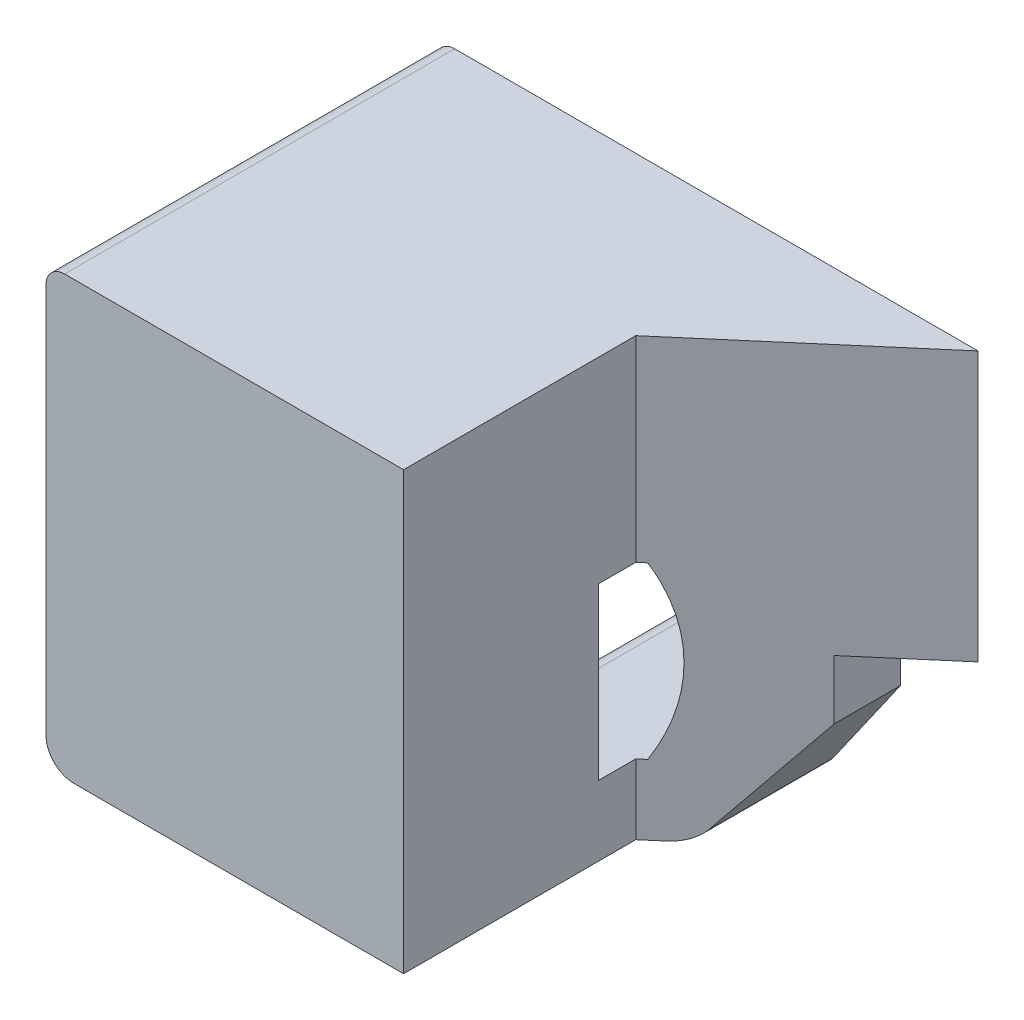
SolidWorks part; units mm, degrees
ref_plane "Front Plane" through (0, 0, 0) normal (0, 0, 1) x (1, 0, 0)
ref_plane "Top Plane" through (0, 0, 0) normal (0, 1, 0) x (1, 0, 0)
ref_plane "Right Plane" through (0, 0, 0) normal (1, 0, 0) x (0, 0, -1)
sketch "Sketch1" plane through (0, 0, 0) normal (0, 0, 1) x (1, 0, 0)
  line L1 (-14.859, 11.938) -> (0, 11.938)
  line L2 (-14.859, 11.938) -> (-14.859, 0)
  line L3 (-14.859, 0) -> (-3.175, 0)
  line L4 (0, 11.938) -> (0, 4.572)
  line L7 (0, 4.572) -> (-3.175, 4.572)
  line L8 (-3.175, 0) -> (-3.175, 4.572)
  dimension "D1" = 11.684
  dimension "D2" = 7.366
  dimension "D3" = 14.859
  dimension "D4" = 11.938
extrude "Extrude1" add sketch "Sketch1" against normal blind 4.7752
sketch "Sketch2" plane through (0, 11.938, 0) normal (0, 1, 0) x (1, 0, 0)
  line L0 (0, 0.5842) -> (-4.191, 4.7752)
  line L1 (0, 4.7752) -> (0, 0) construction
  line L2 (0, 4.7752) -> (-14.859, 4.7752) construction
  line L3 (-4.191, 4.7752) -> (0, 4.7752)
  line L4 (0, 4.7752) -> (0, 0.5842)
  dimension "D1" = 45
  dimension "D2" = 0.5842
extrude "Extrude2" cut sketch "Sketch2" against normal through all
sketch "Sketch33" plane through (-14.859, 0, 0) normal (-1, 0, 0) x (0, 0, 1)
  line L1 (-4.7752, 11.938) -> (-7.0612, 11.938)
  line L2 (-4.7752, 11.938) -> (-4.7752, 6.35)
  line L3 (-4.7752, 6.35) -> (-7.0612, 6.35)
  line L4 (-7.0612, 11.938) -> (-7.0612, 6.35)
  dimension "D1" = 5.588
  dimension "D2" = 2.286
extrude "Extrude30" add sketch "Sketch33" against normal up to vertex (10.668 mm away) up to point (-4.191, 11.938, -4.7752)
sketch "Unlocked" plane through (0, 0, 0) normal (0, 0, 1) x (1, 0, 0)
  circle A0 centre (-9.7028, 4.2418) radius 4.191
  dimension "D3" = 8.382
  dimension "D1" = 2.1082
  dimension "D2" = 5.1562
sketch "End Pressure" plane through (0, 0, 0) normal (0, 0, 1) x (1, 0, 0)
  circle A0 centre (-11.4808, 4.2418) radius 4.191
  dimension "D2" = 8.382
  dimension "D1" = 1.778
sketch "No End Pressure" plane through (0, 0, 0) normal (0, 0, 1) x (1, 0, 0)
  circle A0 centre (-11.9888, 4.2418) radius 4.191
  dimension "D1" = 8.382
  dimension "D2" = 0.508
sketch "Wide Arc" plane through (0, 0, 0) normal (0, 0, 1) x (1, 0, 0)
  circle A10 centre (-11.4808, 4.2418) radius 4.572
  arc A11 (-11.7348, -0.3231) -> (-11.7348, 8.8067) centre (-11.4808, 4.2418) ccw
  circle A13 centre (-11.9888, 4.2418) radius 4.572
  arc A14 (-11.7348, 8.8067) -> (-11.7348, -0.3231) centre (-11.9888, 4.2418) ccw
  dimension "D1" = 0.381
  dimension "D2" = 0.381
sketch "Sketch5" plane through (0, 0, 0) normal (0, 0, 1) x (1, 0, 0)
  line L0 (-14.859, 0) -> (-3.175, 0) construction
  line L1 (-8.962, -0.141) -> (-11.1845, -0.5167) construction
  line L2 (-9.0043, 0.1094) -> (-11.2268, -0.2663) construction
  line L5 (-14.859, 11.938) -> (-14.859, 0) construction
  line L8 (-14.859, 8.1215) -> (-14.859, 0)
  line L9 (-14.859, 0) -> (-8.3742, 0)
  circle A0 centre (-9.7028, 4.2418) radius 4.191 construction
  arc A1 (-9.0043, 0.1094) -> (-8.3436, 8.2063) centre (-9.7028, 4.2418) ccw construction
  arc A2 (-8.3742, 0) -> (-8.2612, 8.4465) centre (-9.7028, 4.2418) ccw
  arc A3 (-8.3436, 8.2063) -> (-11.9888, 8.8138) centre (-11.9888, -2.4257) ccw construction
  arc A4 (-11.7348, 8.8067) -> (-11.7348, -0.3231) centre (-11.9888, 4.2418) ccw construction
  arc A5 (-8.2612, 8.4465) -> (-11.9888, 9.0678) centre (-11.9888, -2.4257) ccw
  arc A6 (-11.9888, 9.0678) -> (-14.859, 8.1215) centre (-11.9888, 4.2418) ccw
  arc A7 (-11.9888, 8.8138) -> (-11.2268, -0.2663) centre (-11.9888, 4.2418) ccw construction
  arc A9 (-8.962, -0.141) -> (-8.2612, 8.4465) centre (-9.7028, 4.2418) ccw construction
  dimension "D1" = 0.254
extrude "Extrude3" cut sketch "Sketch5" against normal blind 3.0988
sketch "Sketch8" plane through (0, 0, 0) normal (0, 0, 1) x (1, 0, 0)
  line L0 (-5.9161, 6.5697) -> (-7.9958, 6.5697)
  line L1 (-8.8371, 7.4938) -> (-8.8371, 8.6017)
  circle A0 centre (-11.4808, 4.2418) radius 4.191 construction
  arc A1 (-7.9958, 6.5697) -> (-8.8371, 7.4938) centre (-11.4808, 4.2418) ccw
  arc A3 (-5.9161, 6.5697) -> (-8.8371, 8.6017) centre (-9.7028, 4.2418) ccw
  arc A5 (-8.3742, 0) -> (-8.2612, 8.4465) centre (-9.7028, 4.2418) ccw construction
  dimension "D1" = 2.921
  dimension "D2" = 2.032
extrude "Extrude6" add sketch "Sketch8" against normal up to surface (3.0988 mm away) up to face at (-11.0666, 5.1959, -3.0988)
sketch "Sketch9" plane through (0, 0, 0) normal (0, 0, 1) x (1, 0, 0)
  line L0 (-5.9161, 1.9139) -> (-7.9958, 1.9139)
  line L1 (-8.8371, 0) -> (-8.8371, 0.9898)
  line L2 (-8.3742, 0) -> (-8.8371, 0)
  line L3 (-8.8371, -0.1181) -> (-8.8371, 0) construction
  arc A0 (-8.3742, 0) -> (-8.8371, -0.1181) centre (-9.7028, 4.2418) cw construction
  circle A1 centre (-11.4808, 4.2418) radius 4.191 construction
  arc A2 (-8.3742, 0) -> (-5.9161, 1.9139) centre (-9.7028, 4.2418) ccw
  arc A3 (-8.8371, 0.9898) -> (-7.9958, 1.9139) centre (-11.4808, 4.2418) ccw
  arc A4 (-8.3742, 0) -> (-5.9161, 6.5697) centre (-9.7028, 4.2418) ccw construction
  dimension "D1" = 2.921
  dimension "D2" = 2.032
extrude "Extrude7" add sketch "Sketch9" against normal up to surface (3.0988 mm away) up to face at (-9.8151, 6.0773, -3.0988)
sketch "Sketch23" plane through (-8.8371, 0, 0) normal (-1, 0, 0) x (0, 0, 1)
  line L0 (-3.0988, 7.4938) -> (-3.0988, 8.6017) construction
  line L1 (0, 7.4938) -> (-3.0988, 7.4938)
  line L2 (0, 7.4938) -> (0, 8.6272)
  line L3 (0, 8.6272) -> (-3.0988, 8.6272)
  line L4 (-3.0988, 7.4938) -> (-3.0988, 8.6272)
  line L7 (-3.0988, 7.4938) -> (0, 7.4938) construction
extrude "Extrude20" add sketch "Sketch23" against normal blind 2.54
sketch "Sketch18" plane through (0, 0, 0) normal (0, 0, 1) x (1, 0, 0)
  line L0 (-4.9036, 6.5697) -> (-5.9161, 6.5697)
  line L1 (-4.9036, 1.9139) -> (-5.9161, 1.9139)
  line L2 (-7.9958, 6.5697) -> (-5.9161, 6.5697) construction
  line L5 (-5.9161, 1.9139) -> (-7.9958, 1.9139) construction
  arc A2 (-4.9036, 1.9139) -> (-4.9036, 6.5697) centre (-9.7028, 4.2418) ccw
  arc A3 (-5.1588, 1.4483) -> (-5.1588, 7.0353) centre (-9.7028, 4.2418) ccw construction
  arc A4 (-5.9161, 1.9139) -> (-5.9161, 6.5697) centre (-9.7028, 4.2418) ccw
  arc A5 (-5.9161, 1.9139) -> (-5.9161, 6.5697) centre (-9.7028, 4.2418) ccw construction
  dimension "D1" = 0.889
extrude "Extrude16" cut sketch "Sketch18" against normal up to surface (3.0988 mm away) up to face at (-9.4738, 4.6916, -3.0988)
fillet "Fillet1" radius 0.762 1 edges at (0, 8.255, -0.5842)
sketch "Sketch24" plane through (0, 0, 0) normal (0, 0, 1) x (1, 0, 0)
  line L0 (-8.8371, 7.4938) -> (-9.8301, 8.3011)
  line L1 (-8.8371, 9.0678) -> (-8.8371, 7.4938)
  line L2 (-8.8371, 8.6272) -> (-8.8371, 7.4938) construction
  line L3 (-8.8371, 9.0678) -> (-11.9888, 9.0678)
  arc A0 (-7.9958, 6.5697) -> (-8.8371, 7.4938) centre (-11.4808, 4.2418) ccw construction
  arc A6 (-9.8301, 8.3011) -> (-11.9888, 9.0678) centre (-11.9888, 5.6457) ccw
  arc A8 (-11.9888, 9.0678) -> (-14.859, 8.1215) centre (-11.9888, 4.2418) ccw construction
extrude "Extrude21" add sketch "Sketch24" against normal up to surface (3.0988 mm away) up to face at (-9.301, 4.6916, -3.0988)
fillet "Fillet2" radius 0.762 1 edges at (-14.859, 0, -3.937)
sketch "Sketch31" plane through (0, 0, 0) normal (0, 0, 1) x (1, 0, 0)
  line L0 (-3.175, 1.4994) -> (-4.2249, 0)
  line L1 (-3.175, 0) -> (-3.175, 4.572) construction
  line L2 (-8.8371, 0) -> (-3.175, 0) construction
  line L3 (-4.2249, 0) -> (-3.175, 0)
  line L4 (-3.175, 0) -> (-3.175, 1.4994)
  line L5 (-3.175, 1.4994) -> (-1.397, 4.0386) construction
  line L7 (-1.397, 4.0386) -> (-1.397, 4.572) construction
  line L8 (-3.175, 4.572) -> (0, 4.572) construction
  dimension "D1" = 55
  dimension "D2" = 1.778
  dimension "D3" = 0.5334
extrude "Extrude28" cut sketch "Sketch31" against normal through all
sketch "Sketch32" plane through (0, 0, 0) normal (0, 0, 1) x (1, 0, 0)
  line L0 (-3.175, 1.4994) -> (-2.159, 2.9504)
  line L1 (-2.159, 2.9504) -> (-2.159, 4.572)
  line L2 (-3.175, 4.572) -> (0, 4.572) construction
  line L3 (-2.159, 4.572) -> (-3.175, 4.572)
  line L4 (-3.175, 4.572) -> (-3.175, 1.4994)
  line L5 (-2.159, 2.9504) -> (-1.0235, 4.572) construction
  line L6 (-3.175, 1.4994) -> (-4.2249, 0) construction
  dimension "D1" = 1.016
extrude "Extrude29" add sketch "Sketch32" against normal up to surface (2.7432 mm away)
fillet "Fillet3" radius 0.762 1 edges at (-4.2249, 0, -2.3876)
fillet "Fillet4" radius 0.508 3 edges at (-3.0782, 1.6376, 0) (-4.2697, 0.0861, 0) (-6.7293, 0, 0)
fillet "Fillet5" radius 0.508 4 edges at (-9.525, 11.938, -7.0612) (-9.525, 6.35, -7.0612) (-7.4295, 11.938, 0) (-14.859, 11.938, -3.5306)
fillet "Fillet6" radius 0.508 3 edges at (-8.8371, 0.9898, -1.5494) (-7.9958, 1.9139, -1.5494) (-7.9958, 6.5697, -1.5494)
sketch "Sketch35" plane through (0, 0, 0) normal (0, 0, 1) x (1, 0, 0)
  line L0 (0, 4.572) -> (0, 11.43) construction
  line L1 (-14.351, 11.938) -> (-0.0386, 11.938) construction
  circle A0 centre (-6.731, 8.763) radius 1.016
  dimension "D1" = 2.032
  dimension "D2" = 6.731
  dimension "D3" = 3.175
extrude "Extrude32" cut sketch "Sketch35" against normal through all
sketch "Sketch36" [suppressed] plane through (0, 0, 0) normal (0, 0, 1) x (1, 0, 0)
  line L9 (-8.8371, 0.508) -> (-8.8371, 0) construction
  line L10 (-8.8371, 0) -> (-4.6215, 0) construction
  line L11 (-8.8371, 0.7565) -> (-8.8371, 0.508)
  line L12 (-8.8371, 0.508) -> (-4.6215, 0.508)
  line L13 (-4.4135, 0.6163) -> (-2.159, 3.836)
  line L14 (-2.159, 3.836) -> (-2.159, 4.572)
  line L15 (-2.159, 4.572) -> (0, 4.572)
  line L16 (0, 4.572) -> (0, 11.43)
  line L17 (0, 11.43) -> (-14.859, 11.43)
  line L18 (-14.859, 11.43) -> (-14.859, 8.1215)
  line L19 (-9.8301, 8.3011) -> (-8.8371, 7.4938)
  line L20 (-7.734, 6.5697) -> (-4.9036, 6.5697)
  line L21 (-4.9036, 1.9139) -> (-7.734, 1.9139)
  line L22 (-8.8371, 0.7565) -> (-8.8371, 0.508)
  line L23 (-8.8371, 0.508) -> (-4.6215, 0.508)
  line L24 (-4.4135, 0.6163) -> (-2.159, 3.836)
  line L25 (-2.159, 3.836) -> (-2.159, 4.572)
  line L26 (-2.159, 4.572) -> (0, 4.572)
  line L27 (0, 4.572) -> (0, 11.43)
  line L28 (0, 11.43) -> (-14.859, 11.43)
  line L29 (-14.859, 11.43) -> (-14.859, 8.1215)
  line L30 (-9.8301, 8.3011) -> (-8.8371, 7.4938)
  line L31 (-7.734, 6.5697) -> (-4.9036, 6.5697)
  line L32 (-4.9036, 1.9139) -> (-7.734, 1.9139)
  line L33 (-4.6215, 0.508) -> (-8.8371, 0.508) construction
  line L34 (-0.0386, 11.938) -> (-14.351, 11.938)
  line L35 (-14.859, 11.43) -> (0, 11.43)
  line L36 (0, 11.43) -> (0, 11.878)
  line L37 (-0.0386, 11.938) -> (-14.351, 11.938)
  line L38 (-14.859, 11.43) -> (0, 11.43)
  line L39 (0, 11.43) -> (0, 11.878)
  line L40 (-2.159, 2.9504) -> (-2.159, 3.836) construction
  line L41 (-2.159, 3.836) -> (-4.4135, 0.6163) construction
  line L42 (-3.9973, 0.3249) -> (-2.159, 2.9504) construction
  line L43 (-8.8371, 0.508) -> (-8.8371, 0)
  line L44 (-8.8371, 0) -> (-4.6215, 0)
  line L45 (-4.6215, 0.508) -> (-8.8371, 0.508)
  line L46 (-2.159, 2.9504) -> (-2.159, 3.836)
  line L47 (-2.159, 3.836) -> (-4.4135, 0.6163)
  line L48 (-3.9973, 0.3249) -> (-2.159, 2.9504)
  arc A3 (-4.6215, 0) -> (-3.9973, 0.3249) centre (-4.6215, 0.762) ccw construction
  arc A4 (-14.351, 11.938) -> (-14.859, 11.43) centre (-14.351, 11.43) ccw
  arc A5 (-14.351, 11.938) -> (-14.859, 11.43) centre (-14.351, 11.43) ccw
  arc A6 (-4.6215, 0.508) -> (-4.4135, 0.6163) centre (-4.6215, 0.762) ccw construction
  arc A7 (-4.6215, 0) -> (-3.9973, 0.3249) centre (-4.6215, 0.762) ccw
  arc A8 (-4.6215, 0.508) -> (-4.4135, 0.6163) centre (-4.6215, 0.762) ccw
  arc A9 (-8.6698, 1.1333) -> (-8.1391, 1.7125) centre (-11.4808, 4.2418) ccw
  arc A10 (-8.6698, 1.1333) -> (-8.8371, 0.7565) centre (-8.3291, 0.7565) ccw
  arc A11 (-4.6215, 0.508) -> (-4.4135, 0.6163) centre (-4.6215, 0.762) ccw
  arc A12 (-11.9888, 9.0678) -> (-14.859, 8.1215) centre (-11.9888, 4.2418) ccw
  arc A13 (-9.8301, 8.3011) -> (-11.9888, 9.0678) centre (-11.9888, 5.6457) ccw
  arc A14 (-8.1391, 6.7711) -> (-8.8371, 7.4938) centre (-11.4808, 4.2418) ccw
  arc A15 (-8.1391, 6.7711) -> (-7.734, 6.5697) centre (-7.734, 7.0777) ccw
  arc A16 (-4.9036, 1.9139) -> (-4.9036, 6.5697) centre (-9.7028, 4.2418) ccw
  arc A17 (-7.734, 1.9139) -> (-8.1391, 1.7125) centre (-7.734, 1.4059) ccw
  arc A18 (-8.6698, 1.1333) -> (-8.1391, 1.7125) centre (-11.4808, 4.2418) ccw
  arc A19 (-8.6698, 1.1333) -> (-8.8371, 0.7565) centre (-8.3291, 0.7565) ccw
  arc A20 (-4.6215, 0.508) -> (-4.4135, 0.6163) centre (-4.6215, 0.762) ccw
  arc A21 (-11.9888, 9.0678) -> (-14.859, 8.1215) centre (-11.9888, 4.2418) ccw
  arc A22 (-9.8301, 8.3011) -> (-11.9888, 9.0678) centre (-11.9888, 5.6457) ccw
  arc A23 (-8.1391, 6.7711) -> (-8.8371, 7.4938) centre (-11.4808, 4.2418) ccw
  arc A24 (-8.1391, 6.7711) -> (-7.734, 6.5697) centre (-7.734, 7.0777) ccw
  arc A25 (-4.9036, 1.9139) -> (-4.9036, 6.5697) centre (-9.7028, 4.2418) ccw
  arc A26 (-7.734, 1.9139) -> (-8.1391, 1.7125) centre (-7.734, 1.4059) ccw
  spline S2 degree 3 poles (2791.7065, -1060.6437) (-2874.9608, 603.1566) (2940.4697, -163.5031) (-2989.9414, -169.8996) knots -101.513121 -101.513121 -101.513121 -101.513121 95.899421 95.899421 95.899421 95.899421 only from (0, 11.878) to (-0.0386, 11.938)
  spline S3 degree 3 poles (0, 11.878) (0, 11.9182) (-0.0119, 11.938) (-0.0386, 11.938) knots 0 0 0 0 1 1 1 1
  dimension "D1" = 0
  dimension "D2" = 0
sketch "Sketch37" plane through (0, 0, 0) normal (0, 0, 1) x (1, 0, 0)
  line L0 (-8.8371, 0.508) -> (-8.8371, 0) construction
  line L1 (-8.8371, 0) -> (-4.6215, 0) construction
  line L2 (-0.0386, 11.938) -> (-14.351, 11.938) construction
  line L3 (0, 11.43) -> (0, 11.878) construction
  line L4 (-2.159, 2.9504) -> (-2.159, 3.836) construction
  line L5 (-3.9973, 0.3249) -> (-2.159, 2.9504) construction
  line L6 (-8.8371, 0.7565) -> (-8.8371, 0.508) construction
  line L7 (-2.159, 3.836) -> (-2.159, 4.572) construction
  line L8 (-2.159, 4.572) -> (0, 4.572) construction
  line L9 (0, 4.572) -> (0, 11.43) construction
  line L10 (-14.859, 11.43) -> (-14.859, 8.1215) construction
  line L11 (-9.8301, 8.3011) -> (-8.8371, 7.4938) construction
  line L12 (-7.734, 6.5697) -> (-4.9036, 6.5697) construction
  line L13 (-4.9036, 1.9139) -> (-7.734, 1.9139) construction
  line L14 (-8.8371, 0.508) -> (-8.8371, 0)
  line L15 (-8.8371, 0) -> (-4.6215, 0)
  line L16 (-0.0386, 11.938) -> (-14.351, 11.938)
  line L17 (0, 11.43) -> (0, 11.878)
  line L18 (-2.159, 2.9504) -> (-2.159, 3.836)
  line L19 (-3.9973, 0.3249) -> (-2.159, 2.9504)
  line L20 (-8.8371, 0.7565) -> (-8.8371, 0.508)
  line L21 (-2.159, 3.836) -> (-2.159, 4.572)
  line L22 (-2.159, 4.572) -> (0, 4.572)
  line L23 (0, 4.572) -> (0, 11.43)
  line L24 (-14.859, 11.43) -> (-14.859, 8.1215)
  line L25 (-9.8301, 8.3011) -> (-8.8371, 7.4938)
  line L26 (-7.734, 6.5697) -> (-4.9036, 6.5697)
  line L27 (-4.9036, 1.9139) -> (-7.734, 1.9139)
  arc A0 (-4.6215, 0) -> (-3.9973, 0.3249) centre (-4.6215, 0.762) ccw construction
  arc A1 (-14.351, 11.938) -> (-14.859, 11.43) centre (-14.351, 11.43) ccw construction
  arc A2 (-8.6698, 1.1333) -> (-8.1391, 1.7125) centre (-11.4808, 4.2418) ccw construction
  arc A3 (-8.6698, 1.1333) -> (-8.8371, 0.7565) centre (-8.3291, 0.7565) ccw construction
  arc A4 (-11.9888, 9.0678) -> (-14.859, 8.1215) centre (-11.9888, 4.2418) ccw construction
  arc A5 (-9.8301, 8.3011) -> (-11.9888, 9.0678) centre (-11.9888, 5.6457) ccw construction
  arc A6 (-8.1391, 6.7711) -> (-8.8371, 7.4938) centre (-11.4808, 4.2418) ccw construction
  arc A7 (-8.1391, 6.7711) -> (-7.734, 6.5697) centre (-7.734, 7.0777) ccw construction
  arc A8 (-4.9036, 1.9139) -> (-4.9036, 6.5697) centre (-9.7028, 4.2418) ccw construction
  arc A9 (-7.734, 1.9139) -> (-8.1391, 1.7125) centre (-7.734, 1.4059) ccw construction
  arc A10 (-4.6215, 0) -> (-3.9973, 0.3249) centre (-4.6215, 0.762) ccw
  arc A11 (-14.351, 11.938) -> (-14.859, 11.43) centre (-14.351, 11.43) ccw
  arc A12 (-8.6698, 1.1333) -> (-8.1391, 1.7125) centre (-11.4808, 4.2418) ccw
  arc A13 (-8.6698, 1.1333) -> (-8.8371, 0.7565) centre (-8.3291, 0.7565) ccw
  arc A14 (-11.9888, 9.0678) -> (-14.859, 8.1215) centre (-11.9888, 4.2418) ccw
  arc A15 (-9.8301, 8.3011) -> (-11.9888, 9.0678) centre (-11.9888, 5.6457) ccw
  arc A16 (-8.1391, 6.7711) -> (-8.8371, 7.4938) centre (-11.4808, 4.2418) ccw
  arc A17 (-8.1391, 6.7711) -> (-7.734, 6.5697) centre (-7.734, 7.0777) ccw
  arc A18 (-4.9036, 1.9139) -> (-4.9036, 6.5697) centre (-9.7028, 4.2418) ccw
  arc A19 (-7.734, 1.9139) -> (-8.1391, 1.7125) centre (-7.734, 1.4059) ccw
  spline S0 degree 3 poles (2791.7065, -1060.6437) (-2874.9608, 603.1566) (2940.4697, -163.5031) (-2989.9414, -169.8996) knots -101.513121 -101.513121 -101.513121 -101.513121 95.899421 95.899421 95.899421 95.899421 only from (0, 11.878) to (-0.0386, 11.938) construction
  spline S1 degree 3 poles (0, 11.878) (0, 11.9182) (-0.0119, 11.938) (-0.0386, 11.938) knots 0 0 0 0 1 1 1 1
extrude "Boss-Extrude1" add sketch "Sketch37" along normal blind 5.334
sketch "Sketch38" plane through (0, 0, 5.334) normal (0, 0, 1) x (1, 0, 0)
  line L6 (-14.859, 8.1215) -> (-14.859, 0.762)
  line L7 (-14.097, 0) -> (-8.8371, 0)
  line L8 (-8.8371, 0) -> (-8.8371, 0.7565)
  line L9 (-7.734, 1.9139) -> (-4.9036, 1.9139)
  line L10 (-4.9036, 6.5697) -> (-7.734, 6.5697)
  line L11 (-8.8371, 0.7565) -> (-8.8371, 0)
  line L12 (-8.8371, 0) -> (-4.6215, 0)
  line L13 (-3.9973, 0.3249) -> (-2.159, 2.9504)
  line L14 (-2.159, 2.9504) -> (-2.159, 4.572)
  line L15 (-2.159, 4.572) -> (0, 4.572)
  line L16 (0, 4.572) -> (0, 11.878)
  line L17 (-0.0386, 11.938) -> (-14.351, 11.938)
  line L18 (-14.859, 11.43) -> (-14.859, 8.1215)
  line L19 (-9.8301, 8.3011) -> (-8.8371, 7.4938)
  line L20 (-7.734, 6.5697) -> (-4.9036, 6.5697)
  line L21 (-4.9036, 1.9139) -> (-7.734, 1.9139)
  line L22 (-8.8371, 0.7565) -> (-8.8371, 0)
  line L23 (-8.8371, 0) -> (-4.6215, 0)
  line L24 (-3.9973, 0.3249) -> (-2.159, 2.9504)
  line L25 (-2.159, 2.9504) -> (-2.159, 4.572)
  line L26 (-2.159, 4.572) -> (0, 4.572)
  line L27 (0, 4.572) -> (0, 11.878)
  line L28 (-0.0386, 11.938) -> (-14.351, 11.938)
  line L29 (-14.859, 11.43) -> (-14.859, 8.1215)
  line L30 (-9.8301, 8.3011) -> (-8.8371, 7.4938)
  line L31 (-7.734, 6.5697) -> (-4.9036, 6.5697)
  line L32 (-4.9036, 1.9139) -> (-7.734, 1.9139)
  line L33 (-8.8371, 7.4938) -> (-9.8301, 8.3011)
  line L34 (-14.859, 8.1215) -> (-14.859, 0.762)
  line L35 (-14.097, 0) -> (-8.8371, 0)
  line L36 (-8.8371, 0) -> (-8.8371, 0.7565)
  line L37 (-7.734, 1.9139) -> (-4.9036, 1.9139)
  line L38 (-4.9036, 6.5697) -> (-7.734, 6.5697)
  line L39 (-8.8371, 7.4938) -> (-9.8301, 8.3011)
  arc A9 (-14.859, 0.762) -> (-14.097, 0) centre (-14.097, 0.762) ccw
  arc A10 (-4.6215, 0) -> (-3.9973, 0.3249) centre (-4.6215, 0.762) ccw
  arc A11 (-14.351, 11.938) -> (-14.859, 11.43) centre (-14.351, 11.43) ccw
  arc A12 (-11.9888, 9.0678) -> (-14.859, 8.1215) centre (-11.9888, 4.2418) ccw
  arc A13 (-9.8301, 8.3011) -> (-11.9888, 9.0678) centre (-11.9888, 5.6457) ccw
  arc A14 (-8.1391, 6.7711) -> (-8.8371, 7.4938) centre (-11.4808, 4.2418) ccw
  arc A15 (-8.1391, 6.7711) -> (-7.734, 6.5697) centre (-7.734, 7.0777) ccw
  arc A16 (-4.9036, 1.9139) -> (-4.9036, 6.5697) centre (-9.7028, 4.2418) ccw
  arc A17 (-7.734, 1.9139) -> (-8.1391, 1.7125) centre (-7.734, 1.4059) ccw
  arc A18 (-8.6698, 1.1333) -> (-8.1391, 1.7125) centre (-11.4808, 4.2418) ccw
  arc A19 (-8.6698, 1.1333) -> (-8.8371, 0.7565) centre (-8.3291, 0.7565) ccw
  arc A20 (-4.6215, 0) -> (-3.9973, 0.3249) centre (-4.6215, 0.762) ccw
  arc A21 (-14.351, 11.938) -> (-14.859, 11.43) centre (-14.351, 11.43) ccw
  arc A22 (-11.9888, 9.0678) -> (-14.859, 8.1215) centre (-11.9888, 4.2418) ccw
  arc A23 (-9.8301, 8.3011) -> (-11.9888, 9.0678) centre (-11.9888, 5.6457) ccw
  arc A24 (-8.1391, 6.7711) -> (-8.8371, 7.4938) centre (-11.4808, 4.2418) ccw
  arc A25 (-8.1391, 6.7711) -> (-7.734, 6.5697) centre (-7.734, 7.0777) ccw
  arc A26 (-4.9036, 1.9139) -> (-4.9036, 6.5697) centre (-9.7028, 4.2418) ccw
  arc A27 (-7.734, 1.9139) -> (-8.1391, 1.7125) centre (-7.734, 1.4059) ccw
  arc A28 (-8.6698, 1.1333) -> (-8.1391, 1.7125) centre (-11.4808, 4.2418) ccw
  arc A29 (-8.6698, 1.1333) -> (-8.8371, 0.7565) centre (-8.3291, 0.7565) ccw
  arc A30 (-8.6698, 1.1333) -> (-8.8371, 0.7565) centre (-8.3291, 0.7565) ccw
  arc A31 (-8.6698, 1.1333) -> (-8.1391, 1.7125) centre (-11.4808, 4.2418) ccw
  arc A32 (-7.734, 1.9139) -> (-8.1391, 1.7125) centre (-7.734, 1.4059) ccw
  arc A33 (-4.9036, 1.9139) -> (-4.9036, 6.5697) centre (-9.7028, 4.2418) ccw
  arc A34 (-8.1391, 6.7711) -> (-7.734, 6.5697) centre (-7.734, 7.0777) ccw
  arc A35 (-8.1391, 6.7711) -> (-8.8371, 7.4938) centre (-11.4808, 4.2418) ccw
  arc A36 (-9.8301, 8.3011) -> (-11.9888, 9.0678) centre (-11.9888, 5.6457) ccw
  arc A37 (-11.9888, 9.0678) -> (-14.859, 8.1215) centre (-11.9888, 4.2418) ccw
  arc A38 (-14.859, 0.762) -> (-14.097, 0) centre (-14.097, 0.762) ccw
  arc A39 (-8.6698, 1.1333) -> (-8.8371, 0.7565) centre (-8.3291, 0.7565) ccw
  arc A40 (-8.6698, 1.1333) -> (-8.1391, 1.7125) centre (-11.4808, 4.2418) ccw
  arc A41 (-7.734, 1.9139) -> (-8.1391, 1.7125) centre (-7.734, 1.4059) ccw
  arc A42 (-4.9036, 1.9139) -> (-4.9036, 6.5697) centre (-9.7028, 4.2418) ccw
  arc A43 (-8.1391, 6.7711) -> (-7.734, 6.5697) centre (-7.734, 7.0777) ccw
  arc A44 (-8.1391, 6.7711) -> (-8.8371, 7.4938) centre (-11.4808, 4.2418) ccw
  arc A45 (-9.8301, 8.3011) -> (-11.9888, 9.0678) centre (-11.9888, 5.6457) ccw
  arc A46 (-11.9888, 9.0678) -> (-14.859, 8.1215) centre (-11.9888, 4.2418) ccw
  spline S1 degree 3 poles (3753.2978, -1335.1264) (-3851.1097, 781.2341) (3929.388, -251.8948) (-3989.8604, -164.5466) knots -111.599427 -111.599427 -111.599427 -111.599427 105.947613 105.947613 105.947613 105.947613 only from (0, 11.878) to (-0.0386, 11.938)
  spline S2 degree 3 poles (0, 11.878) (0, 11.9182) (-0.0119, 11.938) (-0.0386, 11.938) knots 0 0 0 0 1 1 1 1
  dimension "D1" = 0
  dimension "D2" = 0
extrude "Boss-Extrude2" add sketch "Sketch38" along normal blind 5.334
sketch "Sketch39" plane through (-14.859, 0, 0) normal (-1, 0, 0) x (0, 0, 1)
  line L1 (-7.7688, 12.5022) -> (0, 12.5022)
  line L2 (-7.7688, 12.5022) -> (-7.7688, 0)
  line L3 (-7.7688, 0) -> (0, 0)
  line L4 (0, 12.5022) -> (0, 0)
extrude "Cut-Extrude1" cut sketch "Sketch39" against normal through all
sketch "Sketch40" plane through (0, 11.938, 0) normal (0, 1, 0) x (1, 0, 0)
  line L0 (-5.08, -4.318) -> (-0.0386, 0)
  line L1 (0, -10.668) -> (-5.08, -10.668)
  line L2 (0, -10.668) -> (0, -4.318)
  line L3 (0, -4.318) -> (-5.08, -4.318)
  line L4 (-5.08, -10.668) -> (-5.08, -4.318)
  line L10 (0, 0) -> (-0.0386, 0)
  line L11 (-0.0386, 0) -> (-0.0386, -10.668)
  line L12 (-0.0386, -10.668) -> (0, -10.668)
  line L13 (0, -10.668) -> (0, 0)
  line L14 (0, 0) -> (-0.0386, 0)
  line L15 (-0.0386, 0) -> (-0.0386, -10.668)
  line L16 (-0.0386, -10.668) -> (0, -10.668)
  line L17 (0, -10.668) -> (0, 0)
  line M7 (-14.351, -10.668) -> (-0.0386, -10.668)
  line M8 (-0.0386, -10.668) -> (-0.0386, 0)
  dimension "D1" = 6.35
  dimension "D2" = 5.08
  dimension "D3" = 0
extrude "Cut-Extrude2" cut sketch "Sketch40" against normal through all both and the other way through all contours L3 L0 M8 | L4 L3 M7 M8 | L3 L17 L14 M8 | L2 L3 L1 M8
